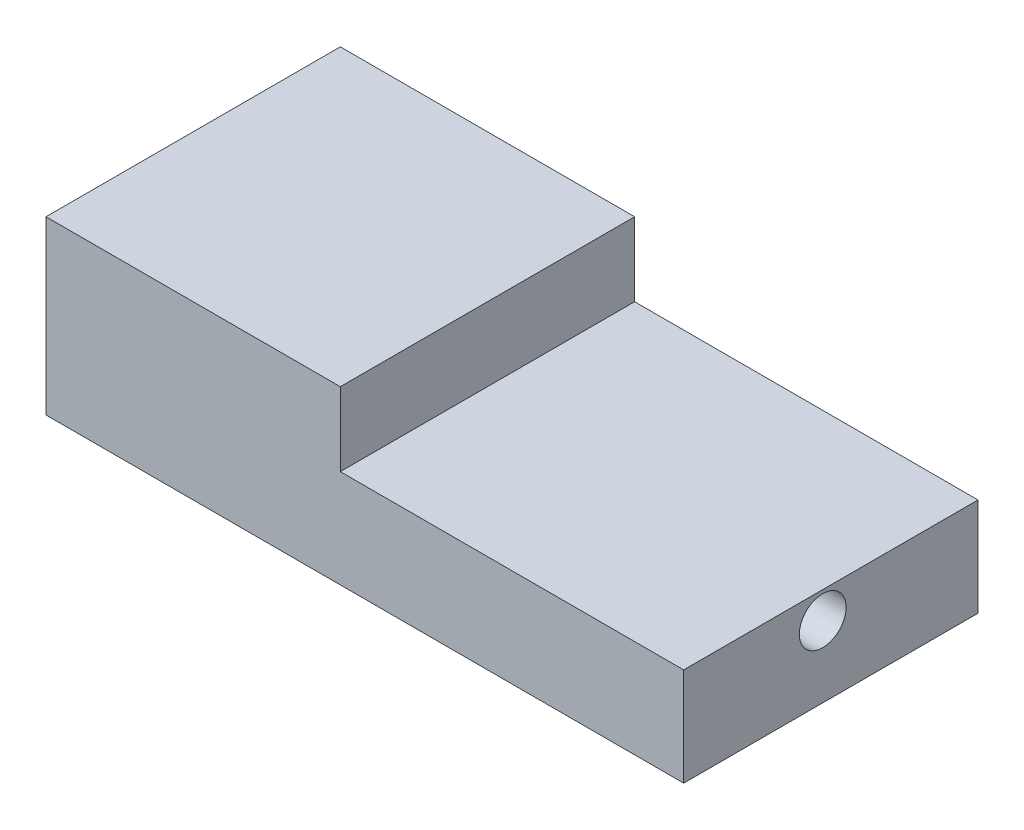
SolidWorks part; units mm, degrees
ref_plane "Front Plane" through (0, 0, 0) normal (0, 0, 1) x (1, 0, 0)
ref_plane "Top Plane" through (0, 0, 0) normal (0, 1, 0) x (1, 0, 0)
ref_plane "Right Plane" through (0, 0, 0) normal (1, 0, 0) x (0, 0, -1)
sketch "Sketch1" plane through (0, 0, 0) normal (1, 0, 0) x (0, 0, -1)
  line L1 (-28.134, 1.866) -> (31.866, 1.866)
  line L2 (-28.134, 1.866) -> (-28.134, -18.134)
  line L3 (-28.134, -18.134) -> (31.866, -18.134)
  line L4 (31.866, 1.866) -> (31.866, -18.134)
  dimension "D1" = 60
  dimension "D2" = 20
extrude "Boss-Extrude1" add sketch "Sketch1" along normal blind 130
sketch "Sketch2" plane through (0, 1.866, 0) normal (0, 1, 0) x (1, 0, 0)
  line L0 (130, -28.134) -> (0, -28.134) construction
  line L1 (0, 31.866) -> (60, 31.866)
  line L2 (0, 31.866) -> (0, -28.134)
  line L3 (0, -28.134) -> (60, -28.134)
  line L4 (60, 31.866) -> (60, -28.134)
  dimension "D1" = 60
extrude "Boss-Extrude2" add sketch "Sketch2" along normal blind 15
sketch "Sketch3" plane through (130, 0, 0) normal (1, 0, 0) x (0, 0, -1)
  circle A0 centre (0.2101, -3.6119) radius 4.7672
extrude "Cut-Extrude1" cut sketch "Sketch3" against normal blind 200
